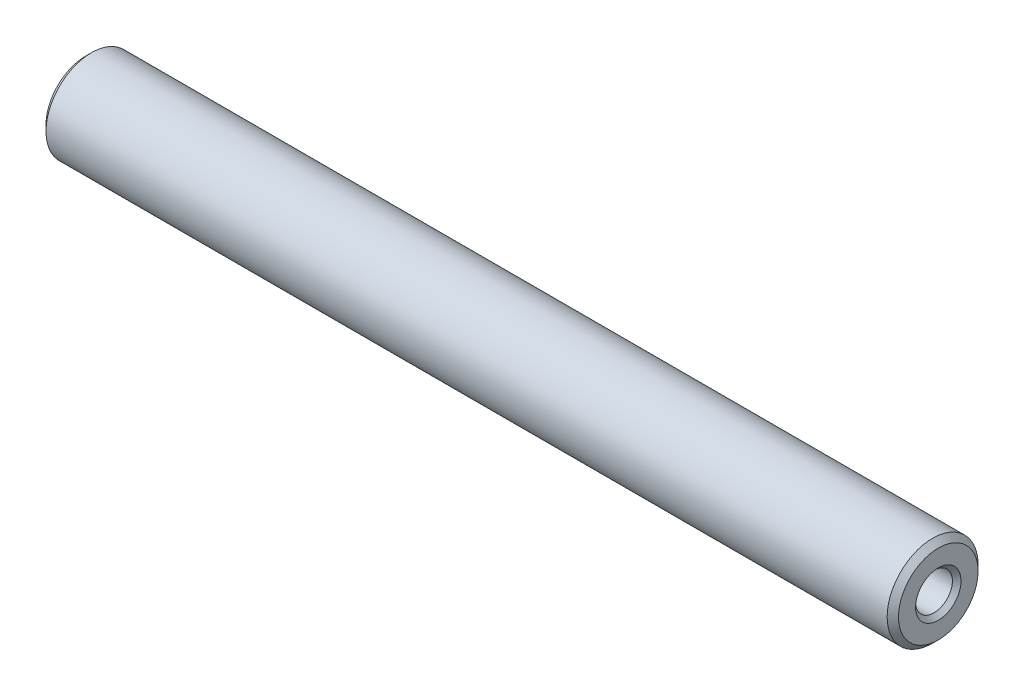
SolidWorks part; units mm, degrees
ref_plane "Front Plane" through (0, 0, 0) normal (0, 0, 1) x (1, 0, 0)
ref_plane "Top Plane" through (0, 0, 0) normal (0, 1, 0) x (1, 0, 0)
ref_plane "Right Plane" through (0, 0, 0) normal (1, 0, 0) x (0, 0, -1)
ref_plane "Plane1" through (0, 0, 0) normal (0, 0, -1) x (-1, 0, 0)
sketch "Sketch1" plane through (0, 0, 0) normal (0, 0, -1) x (-1, 0, 0)
  line L0 (-61.9359, 1.621) -> (-61, 0)
  line L1 (-61, 0) -> (-14, 0)
  line L2 (-14, 0) -> (-13.0641, 1.621)
  line L3 (-13.0641, 1.621) -> (-0.379, 1.621)
  line L4 (-0.379, 1.621) -> (0, 2)
  line L5 (0, 2) -> (0, 3.5)
  line L6 (0, 3.5) -> (-0.5, 4)
  line L7 (-0.5, 4) -> (-74.5, 4)
  line L8 (-74.5, 4) -> (-75, 3.5)
  line L9 (-75, 3.5) -> (-75, 2)
  line L10 (-75, 2) -> (-74.621, 1.621)
  line L11 (-74.621, 1.621) -> (-61.9359, 1.621)
  line L12 (-75, 0) -> (0, 0) construction
revolve "Revolve1" add sketch "Sketch1" angle 360 about L12
